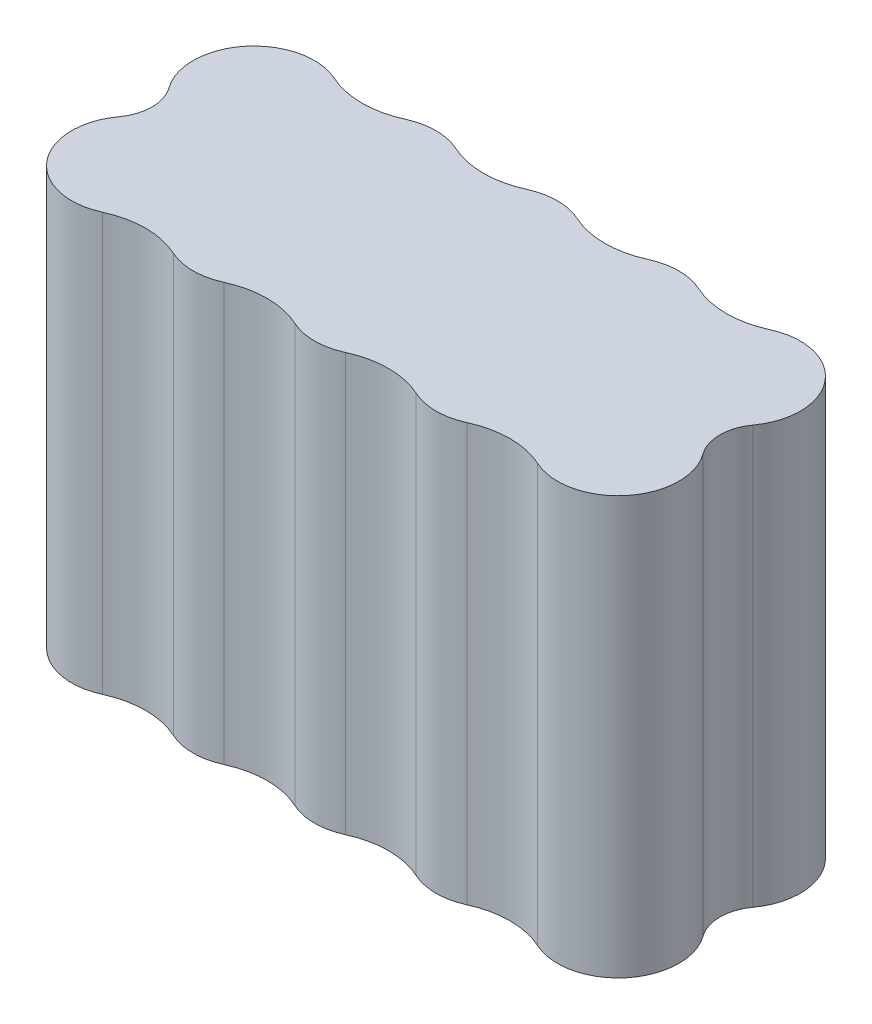
SolidWorks part; units mm, degrees
ref_plane "Front Plane" through (0, 0, 0) normal (0, 0, 1) x (1, 0, 0)
ref_plane "Top Plane" through (0, 0, 0) normal (0, 1, 0) x (1, 0, 0)
ref_plane "Right Plane" through (0, 0, 0) normal (1, 0, 0) x (0, 0, -1)
sketch "Sketch1" plane through (0, 0, 0) normal (0, 1, 0) x (1, 0, 0)
  line L0 (-90.6864, 0) -> (-81.9842, 0) construction
  line L2 (-24.9842, 0) -> (94.8086, 0) construction
  arc A0 (-74.8592, 7.125) -> (-81.9842, 0) centre (-81.9842, 7.125) ccw
  arc A1 (-60.6092, 7.125) -> (-74.8592, 7.125) centre (-67.7342, 7.125) ccw
  arc A2 (-46.3592, 7.125) -> (-60.6092, 7.125) centre (-53.4842, 7.125) ccw
  arc A3 (-32.1092, 7.125) -> (-46.3592, 7.125) centre (-39.2342, 7.125) ccw
  arc A4 (-24.9842, 0) -> (-32.1092, 7.125) centre (-24.9842, 7.125) ccw
  arc A5 (-24.9842, 0) -> (-32.1092, -7.125) centre (-24.9842, -7.125) cw
  arc A6 (-32.1092, -7.125) -> (-46.3592, -7.125) centre (-39.2342, -7.125) cw
  arc A7 (-46.3592, -7.125) -> (-60.6092, -7.125) centre (-53.4842, -7.125) cw
  arc A8 (-60.6092, -7.125) -> (-74.8592, -7.125) centre (-67.7342, -7.125) cw
  arc A9 (-74.8592, -7.125) -> (-81.9842, 0) centre (-81.9842, -7.125) cw
  dimension "D1" = 14.25
  dimension "D2" = 5
extrude "Boss-Extrude1" add sketch "Sketch1" along normal blind 49
fillet "Fillet1" radius 10 8 edges at (-32.1092, 24.5, -7.125) (-46.3592, 24.5, -7.125) (-60.6092, 24.5, -7.125) (-74.8592, 24.5, -7.125) (-32.1092, 24.5, 7.125) (-46.3592, 24.5, 7.125) (-60.6092, 24.5, 7.125) (-74.8592, 24.5, 7.125)
fillet "Fillet2" radius 5 2 edges at (-81.9842, 24.5, 0) (-24.9842, 24.5, 0)
